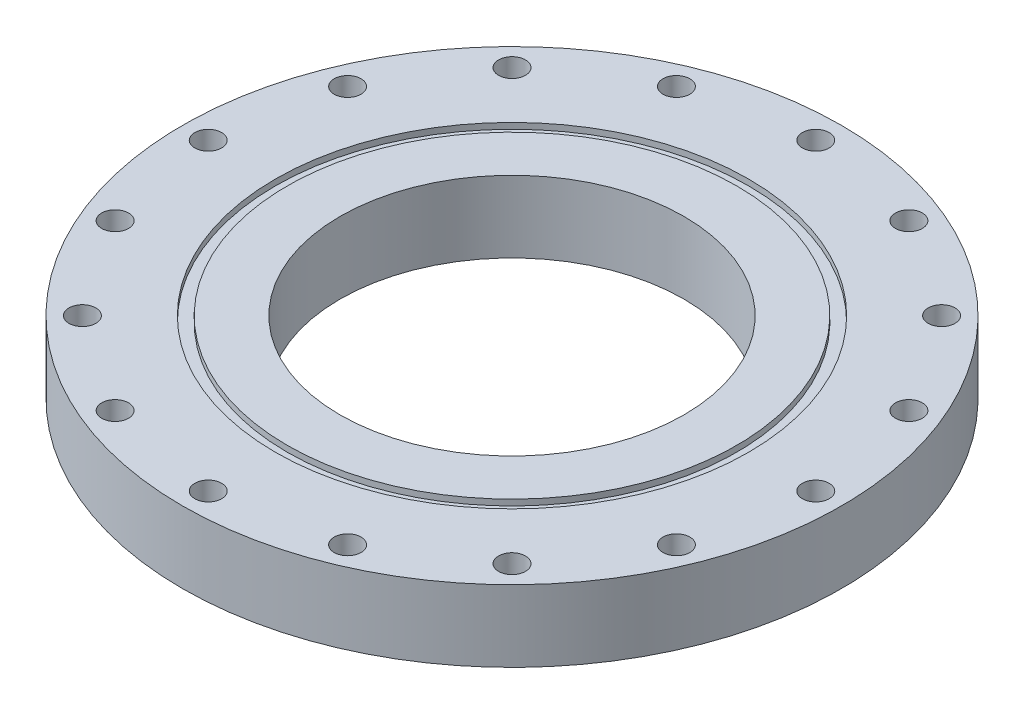
SolidWorks part; units mm, degrees
material "6061-T4 (SS)"
ref_plane "Front Plane" through (0, 0, 0) normal (0, 0, 1) x (1, 0, 0)
ref_plane "Top Plane" through (0, 0, 0) normal (0, 1, 0) x (1, 0, 0)
ref_plane "Right Plane" through (0, 0, 0) normal (1, 0, 0) x (0, 0, -1)
sketch "Sketch1" plane through (0, 0, 0) normal (0, 1, 0) x (1, 0, 0)
  circle A0 centre (0, 0) radius 73.025
  circle A1 centre (0, 0) radius 38.1
  dimension "D1" = 146.05
  dimension "D2" = 76.2
extrude "Boss-Extrude1" add sketch "Sketch1" along normal blind 15.875
sketch "Sketch2" plane through (0, 15.875, 0) normal (0, 1, 0) x (1, 0, 0)
  circle A0 centre (0, 0) radius 67.31 construction
  circle A1 centre (67.31, 0) radius 2.9769
  dimension "D1" = 134.62
  dimension "D2" = 5.9538
extrude "Cut-Extrude1" cut sketch "Sketch2" against normal through all
pattern_circular "CirPattern1" count 16 over 360 about axis through (0, 0, 0) along (0, 1, 0) of "Cut-Extrude1"
sketch "Sketch3" plane through (0, 15.875, 0) normal (0, 1, 0) x (1, 0, 0)
  circle A0 centre (0, 0) radius 49.7967
  circle A1 centre (0, 0) radius 52.4383
  circle A2 centre (0, 0) radius 38.1 construction
  dimension "D1" = 2.6416
  dimension "D2" = 104.8766
extrude "Cut-Extrude2" cut sketch "Sketch3" against normal blind 1.3208
